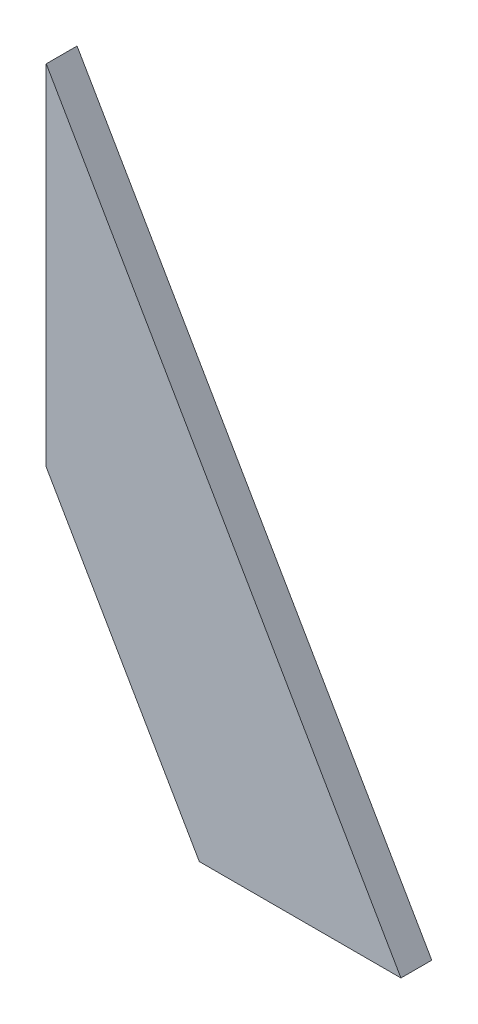
SolidWorks part; units mm, degrees
ref_plane "Front Plane" through (0, 0, 0) normal (0, 0, 1) x (1, 0, 0)
ref_plane "Top Plane" through (0, 0, 0) normal (0, 1, 0) x (1, 0, 0)
ref_plane "Right Plane" through (0, 0, 0) normal (1, 0, 0) x (0, 0, -1)
sketch "Sketch1" plane through (0, 0, 0) normal (0, 0, 1) x (1, 0, 0)
  line L0 (-816.1872, 260.3975) -> (-816.1872, 226.4001)
  line L3 (-816.1872, 226.4001) -> (-801.2864, 200.5912)
  line L4 (-801.2864, 200.5912) -> (-781.658, 200.5912)
  line L5 (-781.658, 200.5912) -> (-816.1872, 260.3975)
extrude "Boss-Extrude1" add sketch "Sketch1" along normal blind 3
